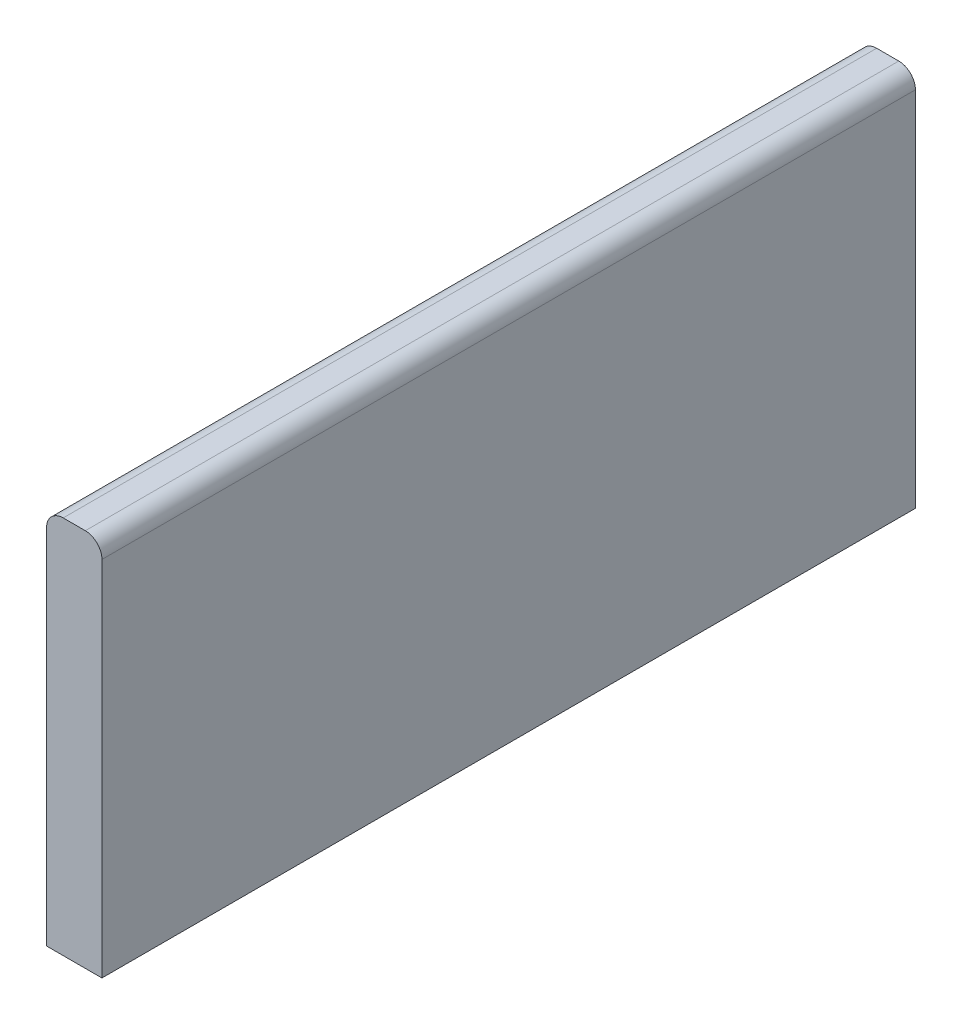
SolidWorks part; units mm, degrees
ref_plane "Plan de face" through (0, 0, 0) normal (0, 0, 1) x (1, 0, 0)
ref_plane "Plan de dessus" through (0, 0, 0) normal (0, 1, 0) x (1, 0, 0)
ref_plane "Plan de droite" through (0, 0, 0) normal (1, 0, 0) x (0, 0, -1)
sketch "Esquisse1" plane through (0, 0, 0) normal (0, 0, 1) x (1, 0, 0)
  line L0 (0, -3) -> (-200, -3) construction
  line L1 (-95, -5) -> (-105, -5)
  line L2 (-95, -5) -> (-95, -73.5)
  line L3 (-95, -73.5) -> (-105, -73.5)
  line L4 (-105, -5) -> (-105, -73.5)
  line L5 (-200, -73.5) -> (0, -73.5) construction
  line L7 (-200, 0) -> (0, 0) construction
  point P8 (-100, -5)
  point P9 (-100, -3)
  point P10 (0, 0)
  point P11 (0, 0)
  point P12 (0, 0)
  dimension "D1" = 10
  dimension "D2" = 5
extrude "Boss.-Extru.1" add sketch "Esquisse1" along normal up to surface (147 mm away)
fillet "Congé1" radius 3 2 edges at (-105, -5, 73.5) (-95, -5, 73.5)
